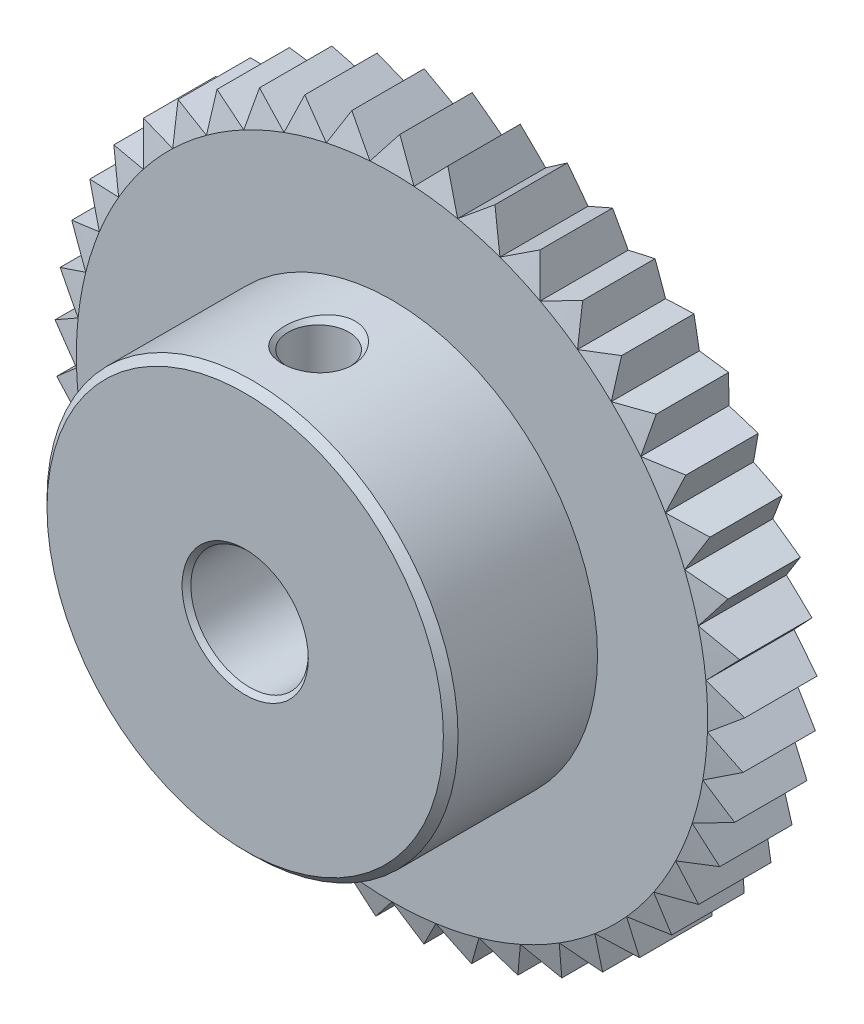
SolidWorks part; units mm, degrees
ref_plane "Front Plane" through (0, 0, 0) normal (0, 0, 1) x (1, 0, 0)
ref_plane "Top Plane" through (0, 0, 0) normal (0, 1, 0) x (1, 0, 0)
ref_plane "Right Plane" through (0, 0, 0) normal (1, 0, 0) x (0, 0, -1)
ref_plane "Plane1" through (0, 0, 0) normal (1, 0, 0) x (0, 0, -1)
sketch "Sketch1" plane through (0, 0, 0) normal (1, 0, 0) x (0, 0, -1)
  line L0 (-16, 4.3) -> (-15.7, 4)
  line L1 (-15.7, 4) -> (-0.3, 4)
  line L2 (-0.3, 4) -> (0, 4.3)
  line L3 (0, 4.3) -> (0, 21.5)
  line L4 (0, 21.5) -> (-0.5359, 23.5)
  line L5 (-0.5359, 23.5) -> (-5.4641, 23.5)
  line L6 (-5.4641, 23.5) -> (-6, 21.5)
  line L7 (-6, 21.5) -> (-6, 14)
  line L8 (-6, 14) -> (-15.5, 14)
  line L9 (-15.5, 14) -> (-16, 13.5)
  line L10 (-16, 13.5) -> (-16, 4.3)
  line L11 (0, 0) -> (-16, 0) construction
revolve "Revolve1" add sketch "Sketch1" angle 360 about L11
ref_plane "Plane2" through (0, 0, 0) normal (0, 0, 1) x (1, 0, 0)
sketch "Sketch2" plane through (0, 0, 0) normal (0, 0, 1) x (1, 0, 0)
  line L0 (-23.4857, 0.8201) -> (-21.4869, -0.7503)
  line L1 (-21.4869, -0.7503) -> (-23.3713, -2.4564)
  line L2 (-23.3713, -2.4564) -> (-21.1734, -3.7334)
  line L3 (-21.1734, -3.7334) -> (-22.8019, -5.6852)
  line L4 (-22.8019, -5.6852) -> (-20.4477, -6.6439)
  line L5 (-20.4477, -6.6439) -> (-21.7888, -8.8033)
  line L6 (-21.7888, -8.8033) -> (-19.3241, -9.425)
  line L7 (-19.3241, -9.425) -> (-20.3516, -11.75)
  line L8 (-20.3516, -11.75) -> (-17.8243, -12.0226)
  line L9 (-17.8243, -12.0226) -> (-18.5183, -14.468)
  line L10 (-18.5183, -14.468) -> (-15.9776, -14.3863)
  line L11 (-15.9776, -14.3863) -> (-16.3245, -16.9045)
  line L12 (-16.3245, -16.9045) -> (-13.8199, -16.47)
  line L13 (-13.8199, -16.47) -> (-13.813, -19.0119)
  line L14 (-13.813, -19.0119) -> (-11.3933, -18.233)
  line L15 (-11.3933, -18.233) -> (-11.0326, -20.7493)
  line L16 (-11.0326, -20.7493) -> (-8.7448, -19.6412)
  line L17 (-8.7448, -19.6412) -> (-8.0375, -22.0828)
  line L18 (-8.0375, -22.0828) -> (-5.9262, -20.6671)
  line L19 (-5.9262, -20.6671) -> (-4.8859, -22.9865)
  line L20 (-4.8859, -22.9865) -> (-2.9922, -21.2908)
  line L21 (-2.9922, -21.2908) -> (-1.6393, -23.4428)
  line L22 (-1.6393, -23.4428) -> (0, -21.5)
  line L23 (0, -21.5) -> (1.6393, -23.4428)
  line L24 (1.6393, -23.4428) -> (2.9922, -21.2908)
  line L25 (2.9922, -21.2908) -> (4.8859, -22.9865)
  line L26 (4.8859, -22.9865) -> (5.9262, -20.6671)
  line L27 (5.9262, -20.6671) -> (8.0375, -22.0828)
  line L28 (8.0375, -22.0828) -> (8.7448, -19.6412)
  line L29 (8.7448, -19.6412) -> (11.0326, -20.7493)
  line L30 (11.0326, -20.7493) -> (11.3933, -18.233)
  line L31 (11.3933, -18.233) -> (13.813, -19.0119)
  line L32 (13.813, -19.0119) -> (13.8199, -16.47)
  line L33 (13.8199, -16.47) -> (16.3245, -16.9045)
  line L34 (16.3245, -16.9045) -> (15.9776, -14.3863)
  line L35 (15.9776, -14.3863) -> (18.5183, -14.468)
  line L36 (18.5183, -14.468) -> (17.8243, -12.0226)
  line L37 (17.8243, -12.0226) -> (20.3516, -11.75)
  line L38 (20.3516, -11.75) -> (19.3241, -9.425)
  line L39 (19.3241, -9.425) -> (21.7888, -8.8033)
  line L40 (21.7888, -8.8033) -> (20.4477, -6.6439)
  line L41 (20.4477, -6.6439) -> (22.8019, -5.6852)
  line L42 (22.8019, -5.6852) -> (21.1734, -3.7334)
  line L43 (21.1734, -3.7334) -> (23.3713, -2.4564)
  line L44 (23.3713, -2.4564) -> (21.4869, -0.7503)
  line L45 (21.4869, -0.7503) -> (23.4857, 0.8201)
  line L46 (23.4857, 0.8201) -> (21.3822, 2.2474)
  line L47 (21.3822, 2.2474) -> (23.143, 4.0807)
  line L48 (23.143, 4.0807) -> (20.8614, 5.2013)
  line L49 (20.8614, 5.2013) -> (22.3498, 7.2619)
  line L50 (22.3498, 7.2619) -> (19.9345, 8.054)
  line L51 (19.9345, 8.054) -> (21.1217, 10.3017)
  line L52 (21.1217, 10.3017) -> (18.6195, 10.75)
  line L53 (18.6195, 10.75) -> (19.4824, 13.141)
  line L54 (19.4824, 13.141) -> (16.9422, 13.2367)
  line L55 (16.9422, 13.2367) -> (17.4639, 15.7246)
  line L56 (17.4639, 15.7246) -> (14.9352, 15.4658)
  line L57 (14.9352, 15.4658) -> (15.1055, 18.002)
  line L58 (15.1055, 18.002) -> (12.6374, 17.3939)
  line L59 (12.6374, 17.3939) -> (12.4531, 19.9291)
  line L60 (12.4531, 19.9291) -> (10.0936, 18.9834)
  line L61 (10.0936, 18.9834) -> (9.5583, 21.4683)
  line L62 (9.5583, 21.4683) -> (7.3534, 20.2034)
  line L63 (7.3534, 20.2034) -> (6.4775, 22.5896)
  line L64 (6.4775, 22.5896) -> (4.4701, 21.0302)
  line L65 (4.4701, 21.0302) -> (3.2706, 23.2713)
  line L66 (3.2706, 23.2713) -> (1.4998, 21.4476)
  line L67 (1.4998, 21.4476) -> (0, 23.5)
  line L68 (0, 23.5) -> (-1.4998, 21.4476)
  line L69 (-1.4998, 21.4476) -> (-3.2706, 23.2713)
  line L70 (-3.2706, 23.2713) -> (-4.4701, 21.0302)
  line L71 (-4.4701, 21.0302) -> (-6.4775, 22.5896)
  line L72 (-6.4775, 22.5896) -> (-7.3534, 20.2034)
  line L73 (-7.3534, 20.2034) -> (-9.5583, 21.4683)
  line L74 (-9.5583, 21.4683) -> (-10.0936, 18.9834)
  line L75 (-10.0936, 18.9834) -> (-12.4531, 19.9291)
  line L76 (-12.4531, 19.9291) -> (-12.6374, 17.3939)
  line L77 (-12.6374, 17.3939) -> (-15.1055, 18.002)
  line L78 (-15.1055, 18.002) -> (-14.9352, 15.4658)
  line L79 (-14.9352, 15.4658) -> (-17.4639, 15.7246)
  line L80 (-17.4639, 15.7246) -> (-16.9422, 13.2367)
  line L81 (-16.9422, 13.2367) -> (-19.4824, 13.141)
  line L82 (-19.4824, 13.141) -> (-18.6195, 10.75)
  line L83 (-18.6195, 10.75) -> (-21.1217, 10.3017)
  line L84 (-21.1217, 10.3017) -> (-19.9345, 8.054)
  line L85 (-19.9345, 8.054) -> (-22.3498, 7.2619)
  line L86 (-22.3498, 7.2619) -> (-20.8614, 5.2013)
  line L87 (-20.8614, 5.2013) -> (-23.143, 4.0807)
  line L88 (-23.143, 4.0807) -> (-21.3822, 2.2474)
  line L89 (-21.3822, 2.2474) -> (-23.4857, 0.8201)
  circle A0 centre (0, 0) radius 47
extrude "Cut-Extrude1" cut sketch "Sketch2" along normal blind 6
ref_plane "Plane3" through (0, 0, 11) normal (0, 0, 1) x (1, 0, 0)
sketch "Sketch3" plane through (0, 0, 11) normal (0, 0, 1) x (1, 0, 0)
  line L0 (0, 0) -> (-2.067, 0)
  line L1 (-2.067, 0) -> (-2.067, 13.567)
  line L2 (-2.067, 13.567) -> (-2.5, 14)
  line L3 (-2.5, 14) -> (-2.5, 15)
  line L4 (-2.5, 15) -> (0, 15)
  line L5 (0, 15) -> (0, 0)
  line L6 (0, 15) -> (0, 0) construction
revolve "Cut-Revolve1" cut sketch "Sketch3" angle 360 about L6
